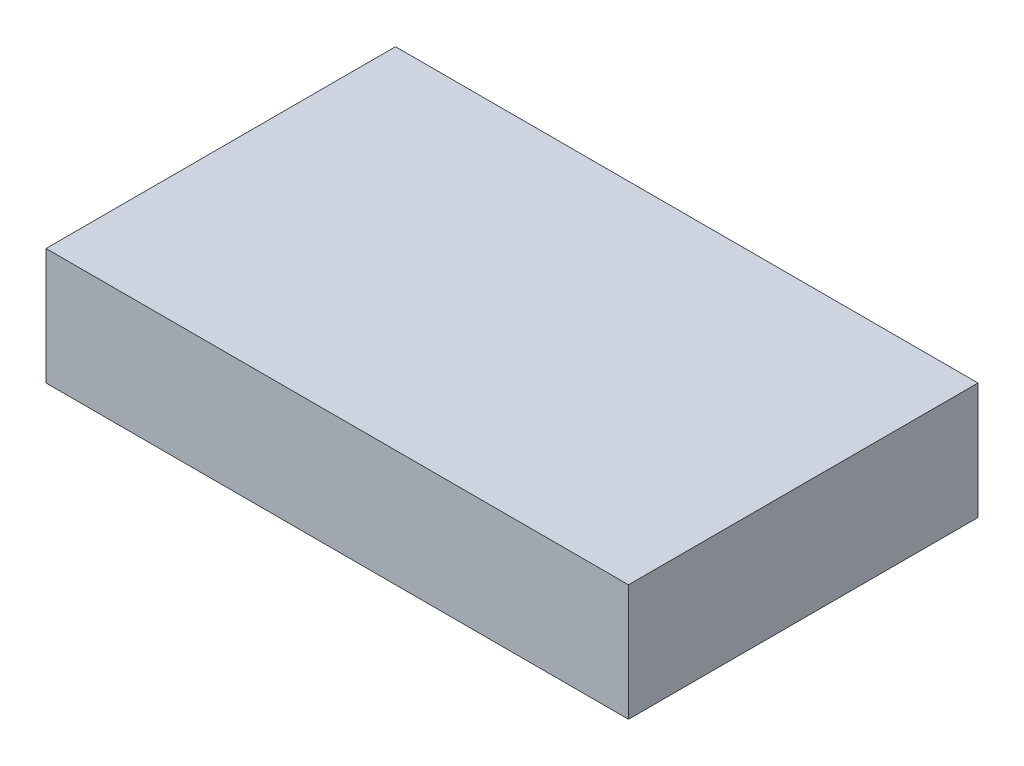
SolidWorks part; units mm, degrees
ref_plane "前视基准面" through (0, 0, 0) normal (0, 0, 1) x (1, 0, 0)
ref_plane "上视基准面" through (0, 0, 0) normal (0, 1, 0) x (1, 0, 0)
ref_plane "右视基准面" through (0, 0, 0) normal (1, 0, 0) x (0, 0, -1)
sketch "草图1" plane through (0, 0, 0) normal (0, 1, 0) x (1, 0, 0)
  line L0 (-154.1262, 0) -> (224.5146, 0) construction
  line L1 (0, -129.551) -> (0, 146.5413) construction
  line L3 (-125, -75) -> (125, -75)
  line L4 (-125, -75) -> (-125, 75)
  line L5 (-125, 75) -> (125, 75)
  line L6 (125, -75) -> (125, 75)
  dimension "D1" = 250
  dimension "D2" = 150
extrude "凸台-拉伸1" add sketch "草图1" along normal blind 50
